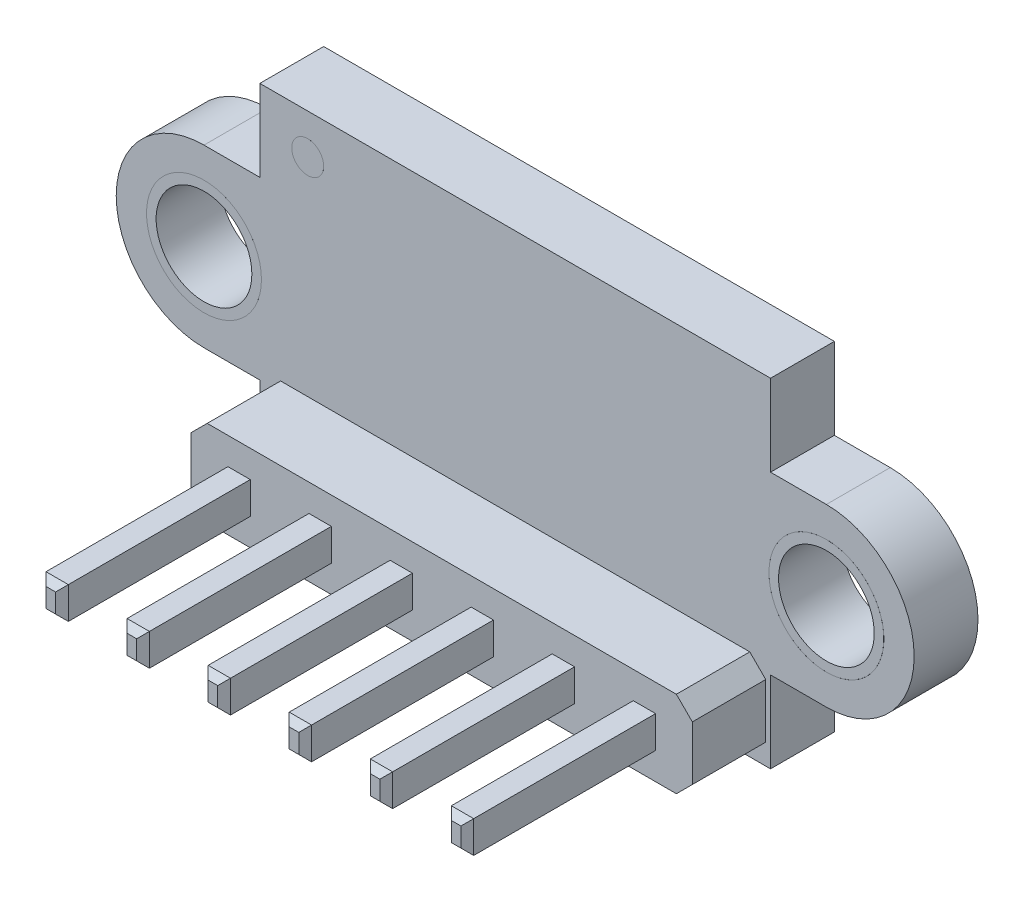
SolidWorks part; units mm, degrees
ref_plane "Plano frontal" through (0, 0, 0) normal (0, 0, 1) x (1, 0, 0)
ref_plane "Plano superior" through (0, 0, 0) normal (0, 1, 0) x (1, 0, 0)
ref_plane "Plano direito" through (0, 0, 0) normal (1, 0, 0) x (0, 0, -1)
sketch "Sketch1" plane through (0, 0, 0) normal (0, 0, 1) x (1, 0, 0)
  line L1 (8, -5.3) -> (-8, -5.3)
  line L2 (8, -5.3) -> (8, 5.3)
  line L3 (8, 5.3) -> (-8, 5.3)
  line L4 (-8, -5.3) -> (-8, 5.3)
  line L5 (8, -5.3) -> (-8, 5.3) construction
  line L6 (8, 5.3) -> (-8, -5.3) construction
  point P0 (0, 0)
  dimension "D1" = 16
  dimension "D2" = 10.6
extrude "Boss-Extrude1" add sketch "Sketch1" along normal mid plane 2
sketch "Sketch2" plane through (0, 0, 0) normal (0, 0, 1) x (1, 0, 0)
  line L0 (0, -5.83) -> (0, 5.83) construction
  line L1 (-9.75, 2.75) -> (-9.75, -2.75) construction
  line L2 (-9.75, 2.75) -> (-8, 2.75)
  line L3 (-8, 5.3) -> (-8, -5.3) construction
  line L4 (-9.75, -2.75) -> (-8, -2.75)
  line L5 (9.75, -2.75) -> (8, -2.75)
  line L6 (9.75, 2.75) -> (8, 2.75)
  line L7 (-8, 2.75) -> (-8, -2.75)
  line L8 (8, 2.75) -> (8, -2.75)
  circle A0 centre (-9.75, 0) radius 1.5
  circle A1 centre (9.75, 0) radius 1.5
  arc A2 (-9.75, 2.75) -> (-9.75, -2.75) centre (-9.75, 0) ccw
  arc A3 (9.75, 2.75) -> (9.75, -2.75) centre (9.75, 0) cw
  dimension "D1" = 3
  dimension "D2" = 25
  dimension "D3" = 1.25
  dimension "D4" = 19.5
extrude "Boss-Extrude2" add sketch "Sketch2" along normal mid plane 2
sketch "Sketch9" plane through (0, 0, -1) normal (0, 0, -1) x (-1, 0, 0)
  line L0 (0, 5.83) -> (0, -5.83) construction
  line L4 (8, 5.3) -> (8, 2.75) construction
  line L6 (-8, 5.3) -> (8, 5.3) construction
  circle A0 centre (-9.75, 0) radius 1.5 construction
  circle A1 centre (-9.75, 0) radius 1.5
  circle A2 centre (-9.75, 0) radius 1.8
  circle A3 centre (9.75, 0) radius 1.8
  circle A4 centre (9.75, 0) radius 1.5
  circle A5 centre (6.5, 4.05) radius 0.5
  dimension "D2" = 1
  dimension "D3" = 1
  dimension "D4" = 0.75
  dimension "D1" = 0.3
extrude "Boss-Extrude9" add sketch "Sketch9" along normal blind 0.0001
mirror "Mirror4" about plane through (0, 0, 0) normal (0, 0, 1) of "Boss-Extrude9"
sketch "Sketch3" plane through (0, 0, 1) normal (0, 0, 1) x (1, 0, 0)
  line L1 (-7.85, -2.45) -> (7.85, -2.45)
  line L2 (-7.85, -2.45) -> (-7.85, -5.15)
  line L3 (-7.85, -5.15) -> (7.85, -5.15)
  line L4 (7.85, -2.45) -> (7.85, -5.15)
  line L5 (-8, -5.3) -> (8, -5.3) construction
  line L6 (-8, -2.75) -> (-8, -5.3) construction
  point P4 (0, -2.45)
  dimension "D1" = 2.7
  dimension "D2" = 0.15
  dimension "D3" = 0.15
  dimension "D4" = 15.7
extrude "Boss-Extrude3" add sketch "Sketch3" along normal blind 2.3
chamfer "Chamfer1" distance 0.5 angle 45 4 edges at (-7.85, -2.45, 2.15) (-7.85, -5.15, 2.15) (7.85, -5.15, 2.15) (7.85, -2.45, 2.15)
sketch "Sketch4" plane through (0, 0, 3.3) normal (0, 0, 1) x (1, 0, 0)
  line L0 (-4.16, -3.3) -> (-3.46, -3.3)
  line L1 (-6.7, -3.3) -> (6.7, -3.3) construction
  line L2 (-6.7, -3.3) -> (-6.7, -4.3) construction
  line L3 (-6.7, -4.3) -> (6.7, -4.3) construction
  line L4 (6.7, -3.3) -> (6.7, -4.3) construction
  line L5 (-7.85, -2.95) -> (-7.85, -4.65) construction
  line L6 (-6.7, -3.3) -> (-6, -3.3)
  line L7 (-6.7, -3.3) -> (-6.7, -4.3)
  line L8 (-6.7, -4.3) -> (-6, -4.3)
  line L9 (-6, -3.3) -> (-6, -4.3)
  line L10 (-4.16, -3.3) -> (-4.16, -4.3)
  line L11 (-4.16, -4.3) -> (-3.46, -4.3)
  line L12 (-3.46, -3.3) -> (-3.46, -4.3)
  line L13 (-1.62, -3.3) -> (-0.92, -3.3)
  line L14 (-1.62, -3.3) -> (-1.62, -4.3)
  line L15 (-1.62, -4.3) -> (-0.92, -4.3)
  line L16 (-0.92, -3.3) -> (-0.92, -4.3)
  line L17 (0.92, -3.3) -> (1.62, -3.3)
  line L18 (0.92, -3.3) -> (0.92, -4.3)
  line L19 (0.92, -4.3) -> (1.62, -4.3)
  line L20 (1.62, -3.3) -> (1.62, -4.3)
  line L21 (3.46, -3.3) -> (4.16, -3.3)
  line L22 (3.46, -3.3) -> (3.46, -4.3)
  line L23 (3.46, -4.3) -> (4.16, -4.3)
  line L24 (4.16, -3.3) -> (4.16, -4.3)
  line L25 (6, -3.3) -> (6.7, -3.3)
  line L26 (6, -3.3) -> (6, -4.3)
  line L27 (6, -4.3) -> (6.7, -4.3)
  line L28 (6.7, -3.3) -> (6.7, -4.3)
  point P4 (0, -3.3)
  point P6 (-7.85, -3.8)
  point P9 (-6.7, -3.8)
  dimension "D1" = 13.4
  dimension "D2" = 1
  dimension "D3" = 0.7
  dimension "D5" = 1.84
  dimension "D4" = 6
extrude "Boss-Extrude4" add sketch "Sketch4" along normal blind 5.9 and the other way blind 6
chamfer "Chamfer3" distance 0.4 angle 45 24 edges at (-1.27, -3.3, -1) (-1.62, -3.8, -1) (-0.92, -3.8, -1) (-1.27, -4.3, -1) (-3.81, -4.3, -1) (-3.46, -3.8, -1) (-3.81, -3.3, -1) (-4.16, -3.8, -1) (-6.35, -3.3, -1) (-6.7, -3.8, -1) (-6, -3.8, -1) (-6.35, -4.3, -1) (1.27, -3.3, -1) (1.62, -3.8, -1) (1.27, -4.3, -1) (0.92, -3.8, -1) (3.46, -3.8, -1) (3.81, -4.3, -1) (4.16, -3.8, -1) (3.81, -3.3, -1) (6.35, -3.3, -1) (6.7, -3.8, -1) (6.35, -4.3, -1) (6, -3.8, -1)
chamfer "Chamfer2" distance 0.2 angle 45 48 edges at (-6.35, -3.3, 9.2) (-6, -3.8, 9.2) (-6.35, -4.3, 9.2) (-6.7, -3.8, 9.2) (6.35, -3.3, 9.2) (6.7, -3.8, 9.2) (6.35, -4.3, 9.2) (6, -3.8, 9.2) (3.81, -3.3, 9.2) (4.16, -3.8, 9.2) (3.81, -4.3, 9.2) (3.46, -3.8, 9.2) (1.27, -3.3, 9.2) (1.62, -3.8, 9.2) (1.27, -4.3, 9.2) (0.92, -3.8, 9.2) (-1.27, -3.3, 9.2) (-0.92, -3.8, 9.2) (-1.27, -4.3, 9.2) (-1.62, -3.8, 9.2) (-3.81, -3.3, 9.2) (-3.46, -3.8, 9.2) (-3.81, -4.3, 9.2) (-4.16, -3.8, 9.2) (-6.35, -4.3, -2.7) (-6, -3.8, -2.7) (-6.35, -3.3, -2.7) (-6.7, -3.8, -2.7) (-3.81, -4.3, -2.7) (-3.46, -3.8, -2.7) (-3.81, -3.3, -2.7) (-4.16, -3.8, -2.7) (-1.27, -4.3, -2.7) (-0.92, -3.8, -2.7) (-1.27, -3.3, -2.7) (-1.62, -3.8, -2.7) (1.27, -4.3, -2.7) (1.62, -3.8, -2.7) (1.27, -3.3, -2.7) (0.92, -3.8, -2.7) (3.81, -4.3, -2.7) (4.16, -3.8, -2.7) (3.81, -3.3, -2.7) (3.46, -3.8, -2.7) (6.35, -4.3, -2.7) (6.7, -3.8, -2.7) (6.35, -3.3, -2.7) (6, -3.8, -2.7)
sketch "Sketch6" plane through (0, 0, -1) normal (0, 0, -1) x (-1, 0, 0)
  line L0 (-8, 5.3) -> (8, 5.3) construction
  line L1 (-2.2, 3.3) -> (2.2, 3.3)
  line L2 (-2.2, 3.3) -> (-2.2, 0.9)
  line L3 (-2.2, 0.9) -> (2.2, 0.9)
  line L4 (2.2, 3.3) -> (2.2, 0.9)
  point P4 (0, 0.9)
  dimension "D1" = 4.4
  dimension "D2" = 2.4
  dimension "D3" = 2
extrude "Boss-Extrude6" add sketch "Sketch6" along normal blind 1.2
sketch "Sketch8" plane through (0, 0, -2.2) normal (0, 0, -1) x (-1, 0, 0)
  line L3 (-2.2, 3.3) -> (-2.2, 0.9) construction
  line L4 (2.2, 0.9) -> (2.2, 3.3) construction
  circle A0 centre (-1.55, 2.1) radius 0.15
  circle A1 centre (1.65, 2.1) radius 0.05
  point P3 (-2.2, 2.1)
  dimension "D1" = 0.3
  dimension "D2" = 0.5
  dimension "D3" = 0.1
  dimension "D4" = 0.5
extrude "Cut-Extrude1" cut sketch "Sketch8" against normal blind 0.01
sketch "Sketch5" plane through (0, 0, -1) normal (0, 0, -1) x (-1, 0, 0)
  line L0 (-2.3, 3.4) -> (-2.3, 0.8)
  line L1 (-2.3, 0.8) -> (2.3, 0.8)
  line L6 (2.3, 0.8) -> (2.3, 3.4)
  line L10 (-2.2, 3.3) -> (-2.2, 0.9)
  line L11 (-2.2, 0.9) -> (2.2, 0.9)
  line L12 (2.2, 0.9) -> (2.2, 3.3)
  line L13 (2.2, 3.3) -> (-2.2, 3.3)
  line L14 (-2.2, 3.3) -> (-2.2, 0.9) construction
  line L15 (-2.2, 0.9) -> (2.2, 0.9) construction
  line L16 (2.2, 0.9) -> (2.2, 3.3) construction
  line L17 (2.2, 3.3) -> (-2.2, 3.3) construction
  line L19 (2.3, 3.4) -> (-2.3, 3.4)
  line L20 (2.4, 3.5) -> (-2.4, 3.5)
  line L21 (-2.4, 3.5) -> (-2.4, 0.7)
  line L22 (-2.4, 0.7) -> (2.4, 0.7)
  line L23 (2.4, 0.7) -> (2.4, 3.5)
  text T0 "VL53L0/1XV2" font "Century Gothic" height 0.75
  dimension "D1" = 0
  dimension "D2" = 0.1
  dimension "D3" = 0.1
extrude "Inscrições" add sketch "Sketch5" along normal blind 0.0001
